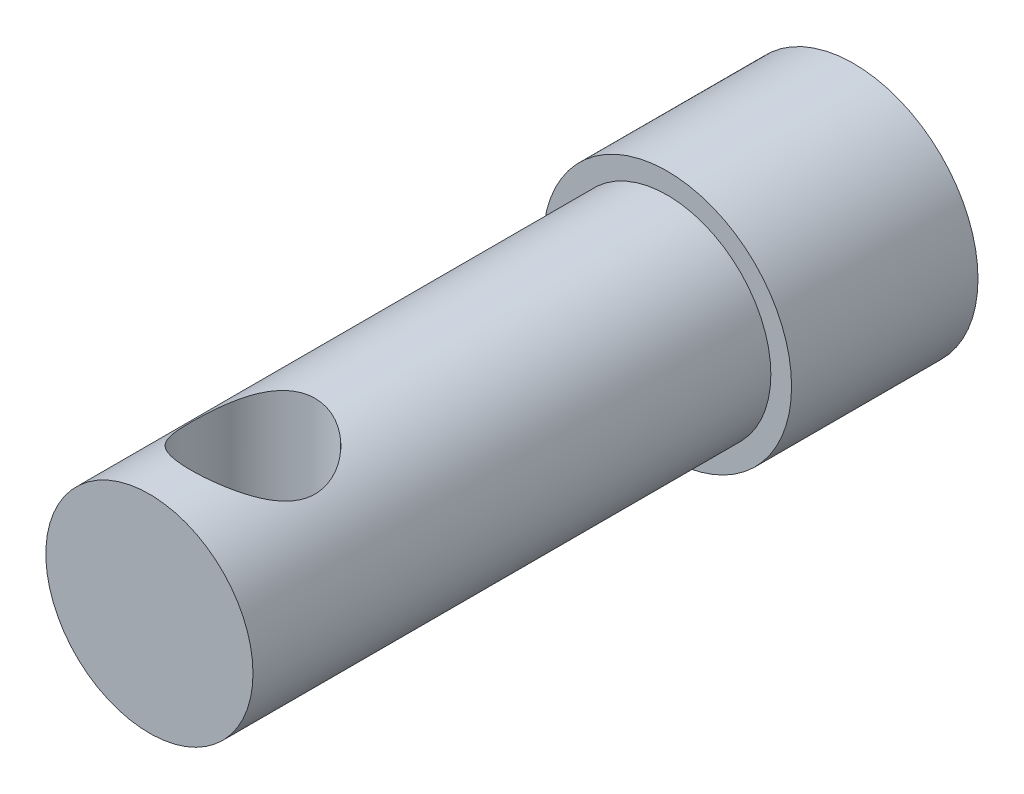
SolidWorks part; units mm, degrees
ref_plane "前视基准面" through (0, 0, 0) normal (0, 0, 1) x (1, 0, 0)
ref_plane "上视基准面" through (0, 0, 0) normal (0, 1, 0) x (1, 0, 0)
ref_plane "右视基准面" through (0, 0, 0) normal (1, 0, 0) x (0, 0, -1)
sketch "草图1" plane through (0, 0, 0) normal (0, 0, 1) x (1, 0, 0)
  circle A0 centre (0, 0) radius 5
  dimension "D1" = 10
extrude "凸台-拉伸1" add sketch "草图1" along normal blind 34
sketch "草图4" plane through (0, 0, 0) normal (0, 0, 1) x (1, 0, 0)
  circle A0 centre (0, 0) radius 6
  dimension "D1" = 12
extrude "凸台-拉伸2" add sketch "草图4" along normal blind 9
sketch "草图2" plane through (0, 0, 0) normal (0, 0, -1) x (-1, 0, 0)
  line L0 (0, 0) -> (0, 3.4851) construction
  line L2 (2.565, -3.165) -> (-2.565, -3.165)
  line L3 (3.165, -2.565) -> (3.165, 2.565)
  line L4 (2.565, 3.165) -> (-2.565, 3.165)
  line L5 (-3.165, -2.565) -> (-3.165, 2.565)
  line L6 (3.165, -3.165) -> (-3.165, 3.165) construction
  line L7 (3.165, 3.165) -> (-3.165, -3.165) construction
  arc A0 (2.565, -3.165) -> (3.165, -2.565) centre (2.565, -2.565) ccw
  arc A1 (-2.565, -3.165) -> (-3.165, -2.565) centre (-2.565, -2.565) cw
  arc A2 (3.165, 2.565) -> (2.565, 3.165) centre (2.565, 2.565) ccw
  arc A3 (-2.565, 3.165) -> (-3.165, 2.565) centre (-2.565, 2.565) ccw
  dimension "D3" = 0.6
  dimension "D1" = 6.33
  dimension "D2" = 6.33
extrude "切除-拉伸1" cut sketch "草图2" against normal blind 8
ref_plane "基准面1" through (0, -5, 0) normal (0, -1, 0) x (-1, 0, 0)
sketch "草图3" plane through (0, -5, 0) normal (0, -1, 0) x (-1, 0, 0)
  line L0 (0, -34) -> (0, -18.3203) construction
  line L1 (-5, -34) -> (5, -34) construction
  circle A0 centre (0, -29) radius 3
  dimension "D2" = 6
  dimension "D1" = 5
extrude "切除-拉伸2" cut sketch "草图3" against normal through all
